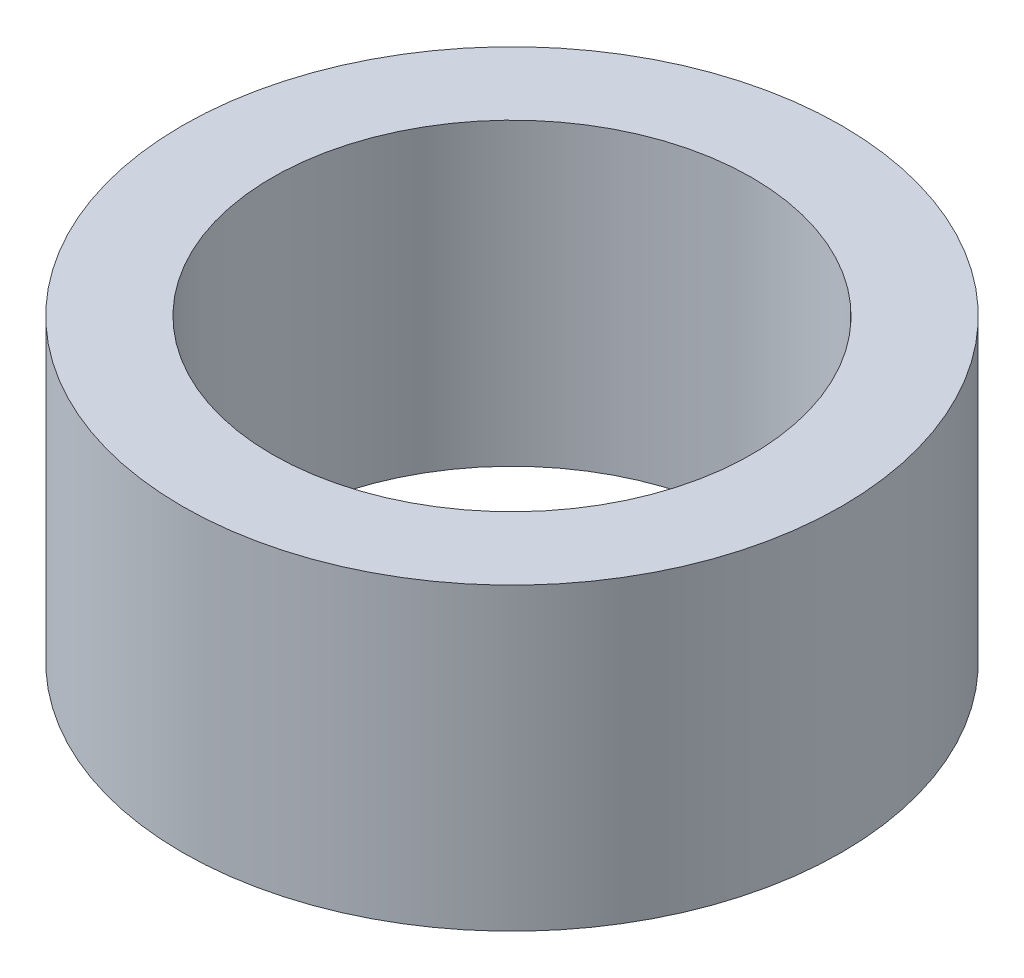
SolidWorks part; units mm, degrees
material "Alloy Steel (SS)"
ref_plane "Front Plane" through (0, 0, 0) normal (0, 0, 1) x (1, 0, 0)
ref_plane "Top Plane" through (0, 0, 0) normal (0, 1, 0) x (1, 0, 0)
ref_plane "Right Plane" through (0, 0, 0) normal (1, 0, 0) x (0, 0, -1)
sketch "Sketch1" plane through (0, 0, 0) normal (0, 1, 0) x (1, 0, 0)
  circle A0 centre (0, 0) radius 4
  circle A1 centre (0, 0) radius 5.5
  dimension "D1" = 11
  dimension "D2" = 8
extrude "Boss-Extrude1" add sketch "Sketch1" along normal mid plane 5
